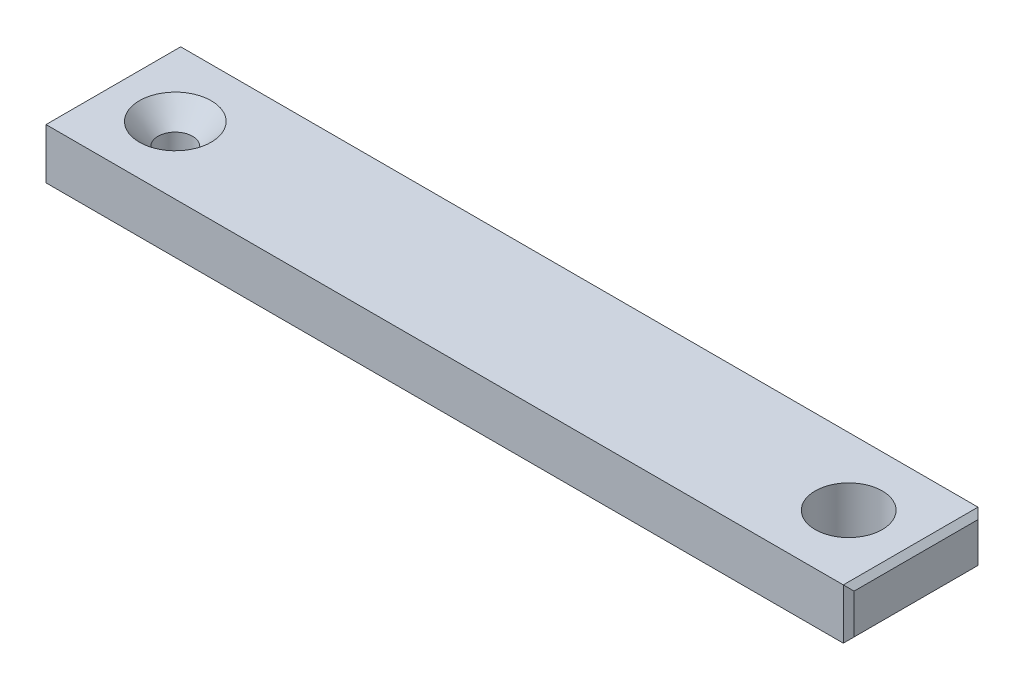
SolidWorks part; units mm, degrees
material "6061-T6 (SS)"
ref_plane "Front Plane" through (0, 0, 0) normal (0, 0, 1) x (1, 0, 0)
ref_plane "Top Plane" through (0, 0, 0) normal (0, 1, 0) x (1, 0, 0)
ref_plane "Right Plane" through (0, 0, 0) normal (1, 0, 0) x (0, 0, -1)
sketch "Sketch1" plane through (0, 0, 0) normal (0, 1, 0) x (1, 0, 0)
  line L0 (-63.5, 0) -> (0, 0) construction
  line L1 (-63.5, 6.35) -> (0, 6.35)
  line L2 (-63.5, -6.35) -> (0, -6.35)
  line L4 (-69.85, 6.35) -> (6.35, 6.35)
  line L5 (-69.85, 6.35) -> (-69.85, -6.35)
  line L6 (-69.85, -6.35) -> (6.35, -6.35)
  line L7 (6.35, 6.35) -> (6.35, -6.35)
  arc A0 (-63.5, 6.35) -> (-63.5, -6.35) centre (-63.5, 0) ccw
  arc A1 (0, -6.35) -> (0, 6.35) centre (0, 0) ccw
  point P2 (-31.75, 0)
  point P9 (-69.85, 0)
  point P10 (6.35, 0)
  dimension "D2" = 76.2
  dimension "D1" = 12.7
extrude "Boss-Extrude2" add sketch "Sketch1" along normal blind 4.7625
sketch "Sketch2" plane through (0, 4.7625, 0) normal (0, 1, 0) x (1, 0, 0)
  line L0 (6.35, 6.35) -> (6.35, -6.35) construction
  line L5 (0, 6.35) -> (0, -6.35)
  line L6 (-69.85, -6.35) -> (6.35, -6.35) construction
  line L7 (-69.85, 6.35) -> (6.35, 6.35) construction
  circle A0 centre (0, 0) radius 3.1623
  dimension "D1" = 6.3246
  dimension "D2" = 6.35
hole_wizard "CSK for #4 Flat Head Socket Cap Screw1" positions "Sketch3" profile "Sketch4" countersink size "#4" standard "ANSI Inch" end condition through all
sketch "Sketch3" plane through (0, 4.7625, 0) normal (0, 1, 0) x (1, 0, 0)
  line L0 (-63.5, 6.35) -> (-63.5, -6.35)
  line L1 (-69.85, 6.35) -> (6.35, 6.35) construction
  line L2 (-69.85, -6.35) -> (6.35, -6.35) construction
  line L4 (-69.85, 6.35) -> (-69.85, -6.35) construction
  point P0 (-63.5, 0)
  dimension "D1" = 6.35
sketch "Sketch4" plane through (-63.5, 4.7625, 0) normal (1, 0, 0) x (0, 0, 1)
  line L0 (0, 0) -> (0, 4.7625)
  line L1 (0, 4.7625) -> (1.6319, 4.7625)
  line L2 (1.6319, 4.7625) -> (1.6319, 2.0234)
  line L3 (1.6319, 2.0234) -> (3.3909, 0)
  line L5 (3.3909, 0) -> (0, 0)
  line L6 (-1.632, 2.0234) -> (-3.3909, 0) construction
  line L11 (0, -6.35) -> (0, 107.95) construction
  dimension "Thru Hole Dia." = 3.2639
  dimension "Thru Hole Depth" = 4.7625
  dimension "Near C'Sink Dia." = 6.7818
  dimension "Near C'Sink Angle" = 82
extrude "Cut-Extrude1" cut sketch "Sketch2" against normal through all contours L5 A0 | L5 A0
chamfer "Chamfer1" distance 0.508 angle 45 8 edges at (-69.85, 2.3813, -6.35) (-69.85, 4.7625, 0) (-69.85, 2.3813, 6.35) (-69.85, 0, 0) (6.35, 2.3813, 6.35) (6.35, 4.7625, 0) (6.35, 2.3813, -6.35) (6.35, 0, 0)
